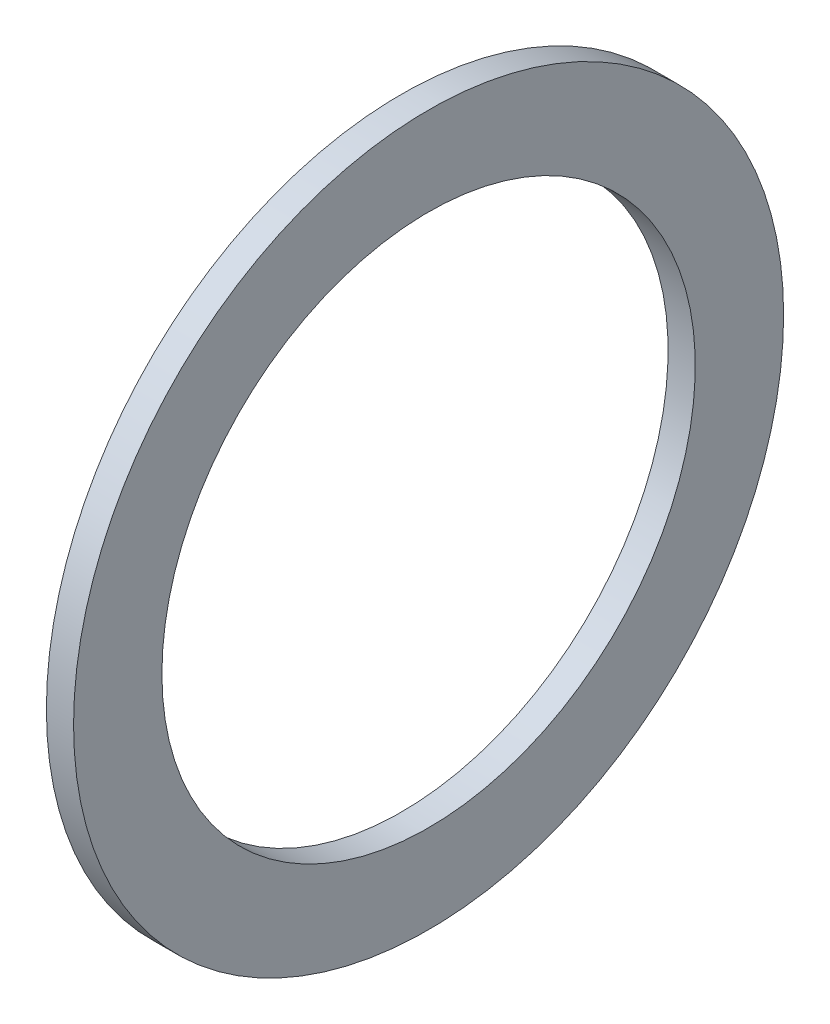
SolidWorks part; units mm, degrees
ref_plane "Front Plane" through (0, 0, 0) normal (0, 0, 1) x (1, 0, 0)
ref_plane "Top Plane" through (0, 0, 0) normal (0, 1, 0) x (1, 0, 0)
ref_plane "Right Plane" through (0, 0, 0) normal (1, 0, 0) x (0, 0, -1)
sketch "Sketch1" plane through (0, 0, 0) normal (0, 0, 1) x (1, 0, 0)
  line L0 (-43.7166, 0) -> (79.6876, 0) construction
  line L2 (0, -19.939) -> (2.032, -19.939)
  line L3 (0, -19.939) -> (0, -26.543)
  line L4 (0, -26.543) -> (2.032, -26.543)
  line L5 (2.032, -19.939) -> (2.032, -26.543)
  dimension "A" = 39.878
  dimension "B" = 53.086
  dimension "C" = 2.032
revolve "Revolve1" add sketch "Sketch1" angle 360 about L0
sketch "Sketch2" [suppressed] plane through (0, 0, 0) normal (0, 0, 1) x (1, 0, 0)
  line L0 (-34.685, 0) -> (47.6686, 0) construction
  circle A0 centre (2.54, -5.715) radius 0.762
  dimension "D1" = 2.54
  dimension "E" = 2.032
  dimension "D" = 35.052
revolve "Revolve3" [suppressed] add sketch "Sketch2" angle 360 about L0
